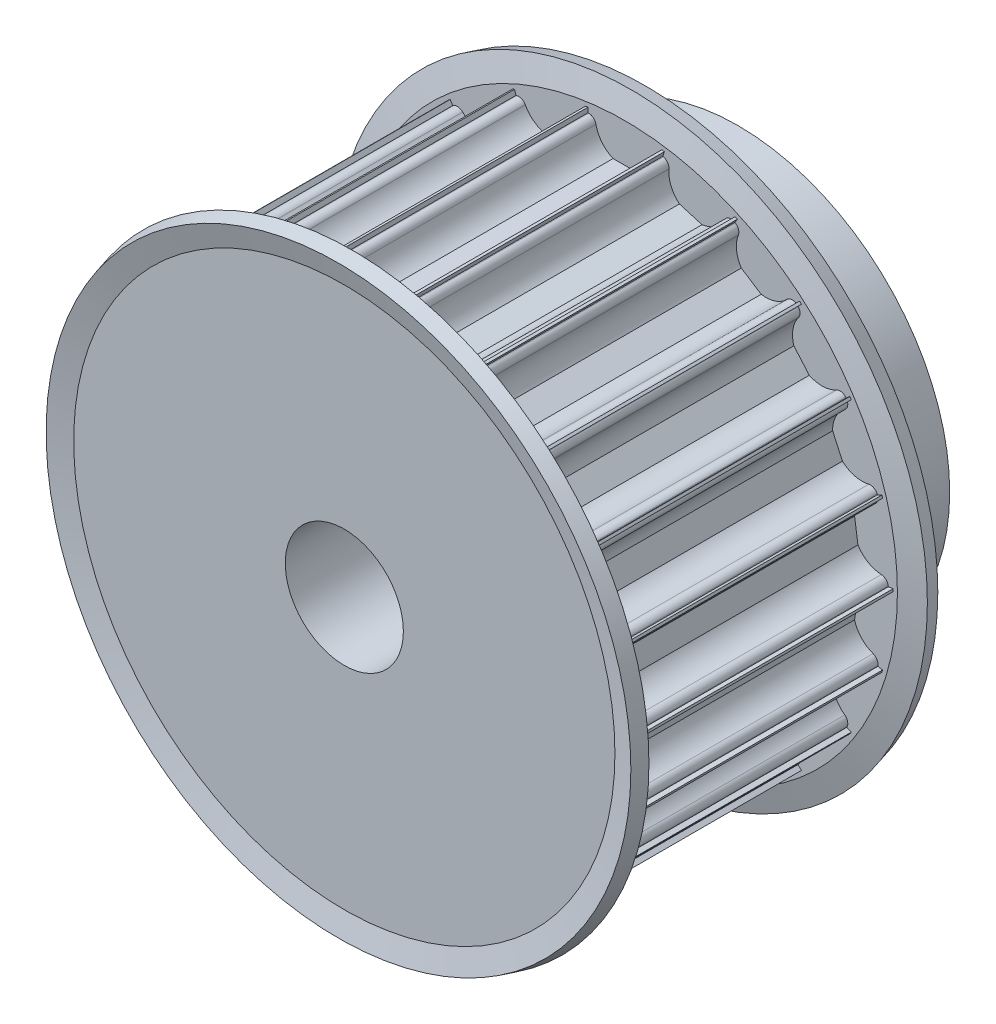
SolidWorks part; units mm, degrees
ref_plane "Front Plane" through (0, 0, 0) normal (0, 0, 1) x (1, 0, 0)
ref_plane "Top Plane" through (0, 0, 0) normal (0, 1, 0) x (1, 0, 0)
ref_plane "Right Plane" through (0, 0, 0) normal (1, 0, 0) x (0, 0, -1)
sketch "Sketch1" plane through (0, 0, 0) normal (1, 0, 0) x (0, 0, -1)
  line L0 (0, 0) -> (34.4325, 0) construction
  line L1 (0, 6) -> (40, 6)
  line L2 (40, 6) -> (40, 21.5)
  line L3 (40, 21.5) -> (30, 21.5)
  line L4 (30, 21.5) -> (30, 27.25)
  line L5 (30, 27.25) -> (0, 27.25)
  line L6 (0, 27.25) -> (0, 6)
  point P5 (0, 0)
  dimension "D1" = 27.25
  dimension "D2" = 6
  dimension "D3" = 30
  dimension "D4" = 10
  dimension "D5" = 15.5
revolve "Revolve1" add sketch "Sketch1" angle 360 about L0
sketch "Sketch2" plane through (0, 0, 0) normal (0, 0, 1) x (1, 0, 0)
  line L0 (-3.6742, 26.5) -> (-3.75, 26.5)
  line L1 (-3.75, 26.5) -> (-3.75, 28.5)
  line L2 (-3.75, 28.5) -> (3.75, 28.5)
  line L3 (3.75, 28.5) -> (3.75, 26.5)
  line L4 (3.75, 26.5) -> (3.6742, 26.5)
  line L5 (-1.199, 23.75) -> (1.199, 23.75)
  arc A0 (2.9394, 25.9) -> (1.199, 23.75) centre (0, 26.5) cw
  arc A1 (2.9394, 25.9) -> (3.6742, 26.5) centre (3.6742, 25.75) cw
  arc A2 (-2.9394, 25.9) -> (-3.6742, 26.5) centre (-3.6742, 25.75) ccw
  arc A3 (-1.199, 23.75) -> (-2.9394, 25.9) centre (0, 26.5) cw
  point P11 (3, 26.5)
  point P14 (-3, 26.5)
  dimension "D1" = 3
  dimension "D3" = 7.5
  dimension "D6" = 0.75
  dimension "D2" = 26.5
  dimension "D4" = 2
  dimension "D5" = 0.75
  dimension "D7" = 2.75
extrude "Cut-Extrude1" cut sketch "Sketch2" against normal up to next (30 mm away)
pattern_circular "CirPattern1" count 22 over 360 about axis through (0, 0, 0) along (0, 0, 1) of "Cut-Extrude1"
sketch "Sketch3" plane through (0, 0, 0) normal (1, 0, 0) x (0, 0, -1)
  line L0 (15, 26.9539) -> (15, 6.5954) construction
  line L1 (30, 26.9539) -> (0, 26.9539) construction
  line L2 (30, 6.5954) -> (0, 6.5954) construction
  line L3 (30, 21.5) -> (30, 27.4925)
  line L4 (30, 27.4925) -> (30.592, 29.7018)
  line L5 (30.592, 29.7018) -> (29.1431, 30.09)
  line L6 (29.1431, 30.09) -> (28.5, 27.69)
  line L7 (28.5, 27.69) -> (28.5, 21.5)
  line L8 (28.5, 21.5) -> (30, 21.5)
  line L9 (1.5, 21.5) -> (0, 21.5)
  line L10 (1.5, 27.69) -> (1.5, 21.5)
  line L11 (-0.592, 29.7018) -> (0.8569, 30.09)
  line L12 (0, 27.4925) -> (-0.592, 29.7018)
  line L13 (0, 21.5) -> (0, 27.4925)
  line L14 (0.8569, 30.09) -> (1.5, 27.69)
  line L15 (0, 0) -> (30, 0) construction
  line L16 (30, -21.5) -> (30, 21.5) construction
  dimension "D1" = 15
  dimension "D2" = 1.5
  dimension "D3" = 6.19
  dimension "D4" = 2.4
revolve "Revolve2" add sketch "Sketch3" angle 360 about L15
